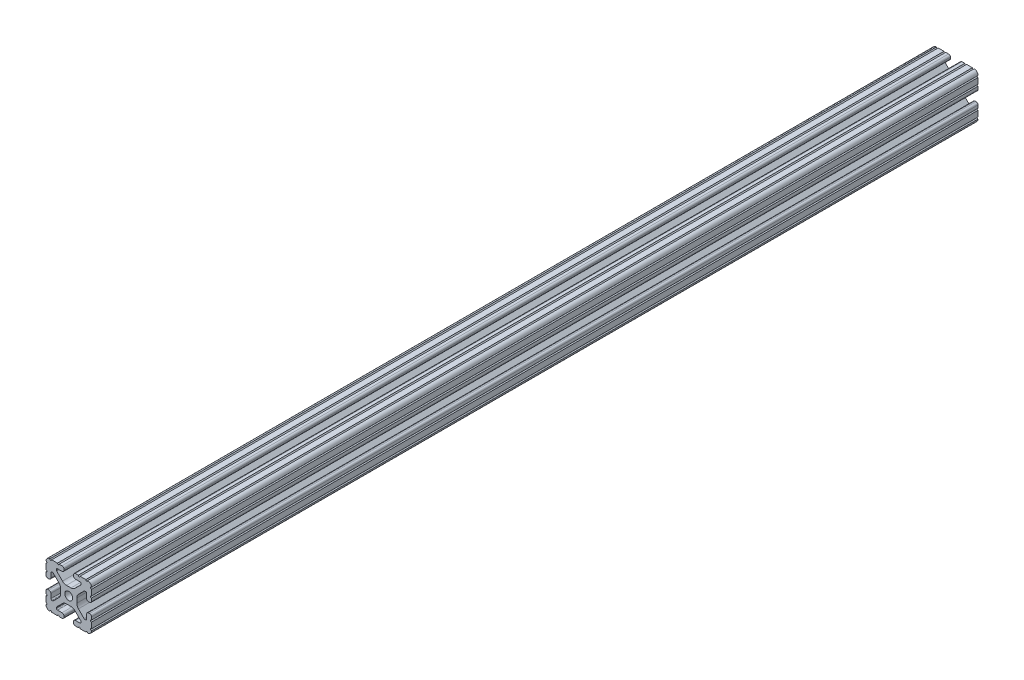
SolidWorks part; units mm, degrees
ref_plane "Front Plane" through (0, 0, 0) normal (0, 0, 1) x (1, 0, 0)
ref_plane "Top Plane" through (0, 0, 0) normal (0, 1, 0) x (1, 0, 0)
ref_plane "Right Plane" through (0, 0, 0) normal (1, 0, 0) x (0, 0, -1)
sketch "Sketch1" plane through (0, 0, 0) normal (0, 0, 1) x (1, 0, 0)
  line L0 (-4.064, 19.05) -> (-4.064, -19.05) construction
  line L1 (-19.05, -19.05) -> (19.05, -19.05) construction
  line L2 (-19.05, -19.05) -> (-19.05, 19.05) construction
  line L3 (-19.05, 19.05) -> (19.05, 19.05) construction
  line L4 (19.05, -19.05) -> (19.05, 19.05) construction
  line L5 (0, 19.05) -> (0, -19.05) construction
  line L6 (-19.05, 0) -> (19.05, 0) construction
  line L7 (-4.064, -19.05) -> (4.064, 19.05) construction
  line L8 (4.064, 19.05) -> (4.064, -19.05) construction
  circle A0 centre (0, 0) radius 3.3274
  point P0 (0, 0)
  line B0 (-10.287, 13.5524) -> (-10.287, 14.0843)
  line B1 (-9.3853, 14.986) -> (-5.6176, 14.986)
  line B2 (-4.064, 16.5396) -> (-4.064, 17.4964)
  line B3 (-5.6176, 19.05) -> (-7.9742, 19.05)
  line B4 (-9.4982, 19.05) -> (-14.3277, 19.05)
  line B5 (-19.05, 14.3277) -> (-19.05, 9.4961)
  line B6 (-19.05, 7.9763) -> (-19.05, 5.6176)
  line B7 (-17.4964, 4.064) -> (-16.5396, 4.064)
  line B8 (-14.986, 5.6176) -> (-14.986, 9.3853)
  line B9 (-14.0843, 10.287) -> (-13.516, 10.287)
  line B10 (-12.8784, 10.0229) -> (-8.1476, 5.2921)
  line B11 (-6.7564, 1.9335) -> (-6.7564, -1.9335)
  line B12 (-8.1476, -5.2921) -> (-12.8784, -10.0229)
  line B13 (-13.516, -10.287) -> (-14.0843, -10.287)
  line B14 (-14.986, -9.3853) -> (-14.986, -5.6176)
  line B15 (-16.5396, -4.064) -> (-17.4964, -4.064)
  line B16 (-19.05, -5.6176) -> (-19.05, -7.9763)
  line B17 (-19.05, -9.4961) -> (-19.05, -14.3277)
  line B18 (-14.3277, -19.05) -> (-9.4961, -19.05)
  line B19 (-7.9763, -19.05) -> (-5.6176, -19.05)
  line B20 (-4.064, -17.4964) -> (-4.064, -16.5396)
  line B21 (-5.6176, -14.986) -> (-9.3853, -14.986)
  line B22 (-10.287, -14.0843) -> (-10.287, -13.5524)
  line B23 (-10.0229, -12.9148) -> (-5.2522, -8.144)
  line B24 (-1.9022, -6.7564) -> (1.9022, -6.7564)
  line B25 (5.2522, -8.144) -> (10.0229, -12.9148)
  line B26 (10.287, -13.5524) -> (10.287, -14.0843)
  line B27 (9.3853, -14.986) -> (5.6176, -14.986)
  line B28 (4.064, -16.5396) -> (4.064, -17.4964)
  line B29 (5.6176, -19.05) -> (7.9763, -19.05)
  line B30 (9.4961, -19.05) -> (14.3277, -19.05)
  line B31 (19.05, -14.3277) -> (19.05, -9.4961)
  line B32 (19.05, -7.9763) -> (19.05, -5.6176)
  line B33 (17.4964, -4.064) -> (16.5396, -4.064)
  line B34 (14.986, -5.6176) -> (14.986, -9.3853)
  line B35 (14.0843, -10.287) -> (13.516, -10.287)
  line B36 (12.8784, -10.0229) -> (8.1476, -5.2921)
  line B37 (6.7564, -1.9335) -> (6.7564, 1.9335)
  line B38 (8.1476, 5.2921) -> (12.8784, 10.0229)
  line B39 (13.516, 10.287) -> (14.0843, 10.287)
  line B40 (14.986, 9.3853) -> (14.986, 5.6176)
  line B41 (16.5396, 4.064) -> (17.4964, 4.064)
  line B42 (19.05, 5.6176) -> (19.05, 7.9763)
  line B43 (19.05, 9.4961) -> (19.05, 14.3277)
  line B44 (14.3277, 19.05) -> (9.4982, 19.05)
  line B45 (7.9742, 19.05) -> (5.6176, 19.05)
  line B46 (4.064, 17.4964) -> (4.064, 16.5396)
  line B47 (5.6176, 14.986) -> (9.3853, 14.986)
  line B48 (10.287, 14.0843) -> (10.287, 13.5524)
  line B49 (10.0229, 12.9148) -> (5.2522, 8.144)
  line B50 (1.9022, 6.7564) -> (-1.9022, 6.7564)
  line B51 (-5.2522, 8.144) -> (-10.0229, 12.9148)
  circle B52 centre (0, 0) radius 3.3274
  arc B53 (-5.6176, 14.986) -> (-4.064, 16.5396) centre (-5.6176, 16.5396) ccw
  arc B54 (-4.064, 17.4964) -> (-5.6176, 19.05) centre (-5.6176, 17.4964) ccw
  arc B55 (-9.4982, 19.05) -> (-7.9742, 19.05) centre (-8.7362, 19.05) ccw
  arc B56 (-15.8475, 19.05) -> (-14.3277, 19.05) centre (-15.0876, 18.9933) ccw
  arc B57 (-15.8475, 19.05) -> (-19.05, 15.8475) centre (-15.8751, 15.8751) ccw
  arc B58 (-19.05, 14.3277) -> (-19.05, 15.8475) centre (-18.9933, 15.0876) ccw
  arc B59 (-19.05, 7.9763) -> (-19.05, 9.4961) centre (-18.9933, 8.7362) ccw
  arc B60 (-19.05, 5.6176) -> (-17.4964, 4.064) centre (-17.4964, 5.6176) ccw
  arc B61 (-16.5396, 4.064) -> (-14.986, 5.6176) centre (-16.5396, 5.6176) ccw
  arc B62 (-14.0843, 10.287) -> (-14.986, 9.3853) centre (-14.0843, 9.3853) ccw
  arc B63 (-12.8784, 10.0229) -> (-13.516, 10.287) centre (-13.516, 9.3853) ccw
  arc B64 (-6.7564, 1.9335) -> (-8.1476, 5.2921) centre (-11.5062, 1.9335) ccw
  arc B65 (-8.1476, -5.2921) -> (-6.7564, -1.9335) centre (-11.5062, -1.9335) ccw
  arc B66 (-13.516, -10.287) -> (-12.8784, -10.0229) centre (-13.516, -9.3853) ccw
  arc B67 (-14.986, -9.3853) -> (-14.0843, -10.287) centre (-14.0843, -9.3853) ccw
  arc B68 (-14.986, -5.6176) -> (-16.5396, -4.064) centre (-16.5396, -5.6176) ccw
  arc B69 (-17.4964, -4.064) -> (-19.05, -5.6176) centre (-17.4964, -5.6176) ccw
  arc B70 (-19.05, -9.4961) -> (-19.05, -7.9763) centre (-18.9933, -8.7362) ccw
  arc B71 (-19.05, -15.8475) -> (-19.05, -14.3277) centre (-18.9933, -15.0876) ccw
  arc B72 (-19.05, -15.8475) -> (-15.8475, -19.05) centre (-15.8751, -15.8751) ccw
  arc B73 (-14.3277, -19.05) -> (-15.8475, -19.05) centre (-15.0876, -18.9933) ccw
  arc B74 (-7.9763, -19.05) -> (-9.4961, -19.05) centre (-8.7362, -18.9933) ccw
  arc B75 (-5.6176, -19.05) -> (-4.064, -17.4964) centre (-5.6176, -17.4964) ccw
  arc B76 (-4.064, -16.5396) -> (-5.6176, -14.986) centre (-5.6176, -16.5396) ccw
  arc B77 (-10.287, -14.0843) -> (-9.3853, -14.986) centre (-9.3853, -14.0843) ccw
  arc B78 (-10.0229, -12.9148) -> (-10.287, -13.5524) centre (-9.3853, -13.5524) ccw
  arc B79 (-1.9022, -6.7564) -> (-5.2522, -8.144) centre (-1.9022, -11.494) ccw
  arc B80 (5.2522, -8.144) -> (1.9022, -6.7564) centre (1.9022, -11.494) ccw
  arc B81 (10.287, -13.5524) -> (10.0229, -12.9148) centre (9.3853, -13.5524) ccw
  arc B82 (9.3853, -14.986) -> (10.287, -14.0843) centre (9.3853, -14.0843) ccw
  arc B83 (5.6176, -14.986) -> (4.064, -16.5396) centre (5.6176, -16.5396) ccw
  arc B84 (4.064, -17.4964) -> (5.6176, -19.05) centre (5.6176, -17.4964) ccw
  arc B85 (9.4961, -19.05) -> (7.9763, -19.05) centre (8.7362, -18.9933) ccw
  arc B86 (15.8475, -19.05) -> (14.3277, -19.05) centre (15.0876, -18.9933) ccw
  arc B87 (15.8475, -19.05) -> (19.05, -15.8475) centre (15.8751, -15.8751) ccw
  arc B88 (19.05, -14.3277) -> (19.05, -15.8475) centre (18.9933, -15.0876) ccw
  arc B89 (19.05, -7.9763) -> (19.05, -9.4961) centre (18.9933, -8.7362) ccw
  arc B90 (19.05, -5.6176) -> (17.4964, -4.064) centre (17.4964, -5.6176) ccw
  arc B91 (16.5396, -4.064) -> (14.986, -5.6176) centre (16.5396, -5.6176) ccw
  arc B92 (14.0843, -10.287) -> (14.986, -9.3853) centre (14.0843, -9.3853) ccw
  arc B93 (12.8784, -10.0229) -> (13.516, -10.287) centre (13.516, -9.3853) ccw
  arc B94 (6.7564, -1.9335) -> (8.1476, -5.2921) centre (11.5062, -1.9335) ccw
  arc B95 (8.1476, 5.2921) -> (6.7564, 1.9335) centre (11.5062, 1.9335) ccw
  arc B96 (13.516, 10.287) -> (12.8784, 10.0229) centre (13.516, 9.3853) ccw
  arc B97 (14.986, 9.3853) -> (14.0843, 10.287) centre (14.0843, 9.3853) ccw
  arc B98 (14.986, 5.6176) -> (16.5396, 4.064) centre (16.5396, 5.6176) ccw
  arc B99 (17.4964, 4.064) -> (19.05, 5.6176) centre (17.4964, 5.6176) ccw
  arc B100 (19.05, 9.4961) -> (19.05, 7.9763) centre (18.9933, 8.7362) ccw
  arc B101 (19.05, 15.8475) -> (19.05, 14.3277) centre (18.9933, 15.0876) ccw
  arc B102 (19.05, 15.8475) -> (15.8475, 19.05) centre (15.8751, 15.8751) ccw
  arc B103 (14.3277, 19.05) -> (15.8475, 19.05) centre (15.0876, 18.9933) ccw
  arc B104 (7.9742, 19.05) -> (9.4982, 19.05) centre (8.7362, 19.05) ccw
  arc B105 (5.6176, 19.05) -> (4.064, 17.4964) centre (5.6176, 17.4964) ccw
  arc B106 (4.064, 16.5396) -> (5.6176, 14.986) centre (5.6176, 16.5396) ccw
  arc B107 (10.287, 14.0843) -> (9.3853, 14.986) centre (9.3853, 14.0843) ccw
  arc B108 (10.0229, 12.9148) -> (10.287, 13.5524) centre (9.3853, 13.5524) ccw
  arc B109 (1.9022, 6.7564) -> (5.2522, 8.144) centre (1.9022, 11.494) ccw
  arc B110 (-5.2522, 8.144) -> (-1.9022, 6.7564) centre (-1.9022, 11.494) ccw
  arc B111 (-10.287, 13.5524) -> (-10.0229, 12.9148) centre (-9.3853, 13.5524) ccw
  dimension "Center Hole Diameter" = 6.6548
  dimension "Rail Width" = 38.1
  dimension "Rail Height" = 38.1
  dimension "T-Slot Width" = 8.128
sketch_block_instance "Block1-1"
sketch_block "Block1"
sketch "Sketch2" plane through (0, 0, 0) normal (1, 0, 0) x (0, 0, -1)
  line L0 (-457.2, 0) -> (457.2, 0) construction
  line L1 (-406.4, 0) -> (-406.4, 19.05) construction
  line L2 (-406.4, 19.05) -> (406.4, 19.05) construction
  line L3 (406.4, 19.05) -> (406.4, 0) construction
  dimension "D1" = 50.8
  dimension "Length" = 914.4
sketch "Sketch3" plane through (0, 0, 0) normal (0, 0, 1) x (1, 0, 0)
  line L0 (-4.064, 16.5396) -> (-4.064, 17.4964) construction
  line L1 (-9.3853, 14.986) -> (-5.6176, 14.986) construction
  line L2 (-10.287, 13.5524) -> (-10.287, 14.0843) construction
  line L3 (-5.2522, 8.144) -> (-10.0229, 12.9148) construction
  line L4 (1.9022, 6.7564) -> (-1.9022, 6.7564) construction
  line L5 (10.0229, 12.9148) -> (5.2522, 8.144) construction
  line L6 (10.287, 14.0843) -> (10.287, 13.5524) construction
  line L7 (5.6176, 14.986) -> (9.3853, 14.986) construction
  line L8 (4.064, 17.4964) -> (4.064, 16.5396) construction
  line L9 (7.9742, 19.05) -> (5.6176, 19.05) construction
  line L10 (14.3277, 19.05) -> (9.4982, 19.05) construction
  line L11 (19.05, 9.4961) -> (19.05, 14.3277) construction
  line L12 (19.05, 5.6176) -> (19.05, 7.9763) construction
  line L13 (16.5396, 4.064) -> (17.4964, 4.064) construction
  line L14 (14.986, 9.3853) -> (14.986, 5.6176) construction
  line L15 (13.516, 10.287) -> (14.0843, 10.287) construction
  line L16 (8.1476, 5.2921) -> (12.8784, 10.0229) construction
  line L17 (6.7564, -1.9335) -> (6.7564, 1.9335) construction
  line L18 (12.8784, -10.0229) -> (8.1476, -5.2921) construction
  line L19 (14.0843, -10.287) -> (13.516, -10.287) construction
  line L20 (14.986, -5.6176) -> (14.986, -9.3853) construction
  line L21 (17.4964, -4.064) -> (16.5396, -4.064) construction
  line L22 (19.05, -7.9763) -> (19.05, -5.6176) construction
  line L23 (19.05, -14.3277) -> (19.05, -9.4961) construction
  line L24 (9.4961, -19.05) -> (14.3277, -19.05) construction
  line L25 (5.6176, -19.05) -> (7.9763, -19.05) construction
  line L26 (4.064, -16.5396) -> (4.064, -17.4964) construction
  line L27 (9.3853, -14.986) -> (5.6176, -14.986) construction
  line L28 (10.287, -13.5524) -> (10.287, -14.0843) construction
  line L29 (5.2522, -8.144) -> (10.0229, -12.9148) construction
  line L30 (-1.9022, -6.7564) -> (1.9022, -6.7564) construction
  line L31 (-10.0229, -12.9148) -> (-5.2522, -8.144) construction
  line L32 (-10.287, -14.0843) -> (-10.287, -13.5524) construction
  line L33 (-5.6176, -14.986) -> (-9.3853, -14.986) construction
  line L34 (-4.064, -17.4964) -> (-4.064, -16.5396) construction
  line L35 (-7.9763, -19.05) -> (-5.6176, -19.05) construction
  line L36 (-14.3277, -19.05) -> (-9.4961, -19.05) construction
  line L37 (-19.05, -9.4961) -> (-19.05, -14.3277) construction
  line L38 (-19.05, -5.6176) -> (-19.05, -7.9763) construction
  line L39 (-16.5396, -4.064) -> (-17.4964, -4.064) construction
  line L40 (-14.986, -9.3853) -> (-14.986, -5.6176) construction
  line L41 (-13.516, -10.287) -> (-14.0843, -10.287) construction
  line L42 (-8.1476, -5.2921) -> (-12.8784, -10.0229) construction
  line L43 (-6.7564, 1.9335) -> (-6.7564, -1.9335) construction
  line L44 (-12.8784, 10.0229) -> (-8.1476, 5.2921) construction
  line L45 (-14.0843, 10.287) -> (-13.516, 10.287) construction
  line L46 (-14.986, 5.6176) -> (-14.986, 9.3853) construction
  line L47 (-17.4964, 4.064) -> (-16.5396, 4.064) construction
  line L48 (-19.05, 7.9763) -> (-19.05, 5.6176) construction
  line L49 (-19.05, 14.3277) -> (-19.05, 9.4961) construction
  line L50 (-9.4982, 19.05) -> (-14.3277, 19.05) construction
  line L51 (-5.6176, 19.05) -> (-7.9742, 19.05) construction
  line L52 (-4.064, 16.5396) -> (-4.064, 17.4964)
  line L53 (-9.3853, 14.986) -> (-5.6176, 14.986)
  line L54 (-10.287, 13.5524) -> (-10.287, 14.0843)
  line L55 (-5.2522, 8.144) -> (-10.0229, 12.9148)
  line L56 (1.9022, 6.7564) -> (-1.9022, 6.7564)
  line L57 (10.0229, 12.9148) -> (5.2522, 8.144)
  line L58 (10.287, 14.0843) -> (10.287, 13.5524)
  line L59 (5.6176, 14.986) -> (9.3853, 14.986)
  line L60 (4.064, 17.4964) -> (4.064, 16.5396)
  line L61 (7.9742, 19.05) -> (5.6176, 19.05)
  line L62 (14.3277, 19.05) -> (9.4982, 19.05)
  line L63 (19.05, 9.4961) -> (19.05, 14.3277)
  line L64 (19.05, 5.6176) -> (19.05, 7.9763)
  line L65 (16.5396, 4.064) -> (17.4964, 4.064)
  line L66 (14.986, 9.3853) -> (14.986, 5.6176)
  line L67 (13.516, 10.287) -> (14.0843, 10.287)
  line L68 (8.1476, 5.2921) -> (12.8784, 10.0229)
  line L69 (6.7564, -1.9335) -> (6.7564, 1.9335)
  line L70 (12.8784, -10.0229) -> (8.1476, -5.2921)
  line L71 (14.0843, -10.287) -> (13.516, -10.287)
  line L72 (14.986, -5.6176) -> (14.986, -9.3853)
  line L73 (17.4964, -4.064) -> (16.5396, -4.064)
  line L74 (19.05, -7.9763) -> (19.05, -5.6176)
  line L75 (19.05, -14.3277) -> (19.05, -9.4961)
  line L76 (9.4961, -19.05) -> (14.3277, -19.05)
  line L77 (5.6176, -19.05) -> (7.9763, -19.05)
  line L78 (4.064, -16.5396) -> (4.064, -17.4964)
  line L79 (9.3853, -14.986) -> (5.6176, -14.986)
  line L80 (10.287, -13.5524) -> (10.287, -14.0843)
  line L81 (5.2522, -8.144) -> (10.0229, -12.9148)
  line L82 (-1.9022, -6.7564) -> (1.9022, -6.7564)
  line L83 (-10.0229, -12.9148) -> (-5.2522, -8.144)
  line L84 (-10.287, -14.0843) -> (-10.287, -13.5524)
  line L85 (-5.6176, -14.986) -> (-9.3853, -14.986)
  line L86 (-4.064, -17.4964) -> (-4.064, -16.5396)
  line L87 (-7.9763, -19.05) -> (-5.6176, -19.05)
  line L88 (-14.3277, -19.05) -> (-9.4961, -19.05)
  line L89 (-19.05, -9.4961) -> (-19.05, -14.3277)
  line L90 (-19.05, -5.6176) -> (-19.05, -7.9763)
  line L91 (-16.5396, -4.064) -> (-17.4964, -4.064)
  line L92 (-14.986, -9.3853) -> (-14.986, -5.6176)
  line L93 (-13.516, -10.287) -> (-14.0843, -10.287)
  line L94 (-8.1476, -5.2921) -> (-12.8784, -10.0229)
  line L95 (-6.7564, 1.9335) -> (-6.7564, -1.9335)
  line L96 (-12.8784, 10.0229) -> (-8.1476, 5.2921)
  line L97 (-14.0843, 10.287) -> (-13.516, 10.287)
  line L98 (-14.986, 5.6176) -> (-14.986, 9.3853)
  line L99 (-17.4964, 4.064) -> (-16.5396, 4.064)
  line L100 (-19.05, 7.9763) -> (-19.05, 5.6176)
  line L101 (-19.05, 14.3277) -> (-19.05, 9.4961)
  line L102 (-9.4982, 19.05) -> (-14.3277, 19.05)
  line L103 (-5.6176, 19.05) -> (-7.9742, 19.05)
  circle A0 centre (0, 0) radius 3.3274 construction
  circle A1 centre (0, 0) radius 3.3274
  circle A2 centre (0, 0) radius 3.3274
  arc A3 (-5.6176, 14.986) -> (-4.064, 16.5396) centre (-5.6176, 16.5396) ccw construction
  arc A4 (-9.3853, 14.986) -> (-10.287, 14.0843) centre (-9.3853, 14.0843) ccw construction
  arc A5 (-10.287, 13.5524) -> (-10.0229, 12.9148) centre (-9.3853, 13.5524) ccw construction
  arc A6 (-5.2522, 8.144) -> (-1.9022, 6.7564) centre (-1.9022, 11.494) ccw construction
  arc A7 (1.9022, 6.7564) -> (5.2522, 8.144) centre (1.9022, 11.494) ccw construction
  arc A8 (10.0229, 12.9148) -> (10.287, 13.5524) centre (9.3853, 13.5524) ccw construction
  arc A9 (10.287, 14.0843) -> (9.3853, 14.986) centre (9.3853, 14.0843) ccw construction
  arc A10 (4.064, 16.5396) -> (5.6176, 14.986) centre (5.6176, 16.5396) ccw construction
  arc A11 (5.6176, 19.05) -> (4.064, 17.4964) centre (5.6176, 17.4964) ccw construction
  arc A12 (7.9742, 19.05) -> (9.4982, 19.05) centre (8.7362, 19.05) ccw construction
  arc A13 (14.3277, 19.05) -> (15.8475, 19.05) centre (15.0876, 18.9933) ccw construction
  arc A14 (19.05, 15.8475) -> (15.8475, 19.05) centre (15.8751, 15.8751) ccw construction
  arc A15 (19.05, 15.8475) -> (19.05, 14.3277) centre (18.9933, 15.0876) ccw construction
  arc A16 (19.05, 9.4961) -> (19.05, 7.9763) centre (18.9933, 8.7362) ccw construction
  arc A17 (17.4964, 4.064) -> (19.05, 5.6176) centre (17.4964, 5.6176) ccw construction
  arc A18 (14.986, 5.6176) -> (16.5396, 4.064) centre (16.5396, 5.6176) ccw construction
  arc A19 (14.986, 9.3853) -> (14.0843, 10.287) centre (14.0843, 9.3853) ccw construction
  arc A20 (13.516, 10.287) -> (12.8784, 10.0229) centre (13.516, 9.3853) ccw construction
  arc A21 (8.1476, 5.2921) -> (6.7564, 1.9335) centre (11.5062, 1.9335) ccw construction
  arc A22 (6.7564, -1.9335) -> (8.1476, -5.2921) centre (11.5062, -1.9335) ccw construction
  arc A23 (12.8784, -10.0229) -> (13.516, -10.287) centre (13.516, -9.3853) ccw construction
  arc A24 (14.0843, -10.287) -> (14.986, -9.3853) centre (14.0843, -9.3853) ccw construction
  arc A25 (16.5396, -4.064) -> (14.986, -5.6176) centre (16.5396, -5.6176) ccw construction
  arc A26 (19.05, -5.6176) -> (17.4964, -4.064) centre (17.4964, -5.6176) ccw construction
  arc A27 (19.05, -7.9763) -> (19.05, -9.4961) centre (18.9933, -8.7362) ccw construction
  arc A28 (19.05, -14.3277) -> (19.05, -15.8475) centre (18.9933, -15.0876) ccw construction
  arc A29 (15.8475, -19.05) -> (19.05, -15.8475) centre (15.8751, -15.8751) ccw construction
  arc A30 (15.8475, -19.05) -> (14.3277, -19.05) centre (15.0876, -18.9933) ccw construction
  arc A31 (9.4961, -19.05) -> (7.9763, -19.05) centre (8.7362, -18.9933) ccw construction
  arc A32 (4.064, -17.4964) -> (5.6176, -19.05) centre (5.6176, -17.4964) ccw construction
  arc A33 (5.6176, -14.986) -> (4.064, -16.5396) centre (5.6176, -16.5396) ccw construction
  arc A34 (9.3853, -14.986) -> (10.287, -14.0843) centre (9.3853, -14.0843) ccw construction
  arc A35 (10.287, -13.5524) -> (10.0229, -12.9148) centre (9.3853, -13.5524) ccw construction
  arc A36 (5.2522, -8.144) -> (1.9022, -6.7564) centre (1.9022, -11.494) ccw construction
  arc A37 (-1.9022, -6.7564) -> (-5.2522, -8.144) centre (-1.9022, -11.494) ccw construction
  arc A38 (-10.0229, -12.9148) -> (-10.287, -13.5524) centre (-9.3853, -13.5524) ccw construction
  arc A39 (-10.287, -14.0843) -> (-9.3853, -14.986) centre (-9.3853, -14.0843) ccw construction
  arc A40 (-4.064, -16.5396) -> (-5.6176, -14.986) centre (-5.6176, -16.5396) ccw construction
  arc A41 (-5.6176, -19.05) -> (-4.064, -17.4964) centre (-5.6176, -17.4964) ccw construction
  arc A42 (-7.9763, -19.05) -> (-9.4961, -19.05) centre (-8.7362, -18.9933) ccw construction
  arc A43 (-14.3277, -19.05) -> (-15.8475, -19.05) centre (-15.0876, -18.9933) ccw construction
  arc A44 (-19.05, -15.8475) -> (-15.8475, -19.05) centre (-15.8751, -15.8751) ccw construction
  arc A45 (-19.05, -15.8475) -> (-19.05, -14.3277) centre (-18.9933, -15.0876) ccw construction
  arc A46 (-19.05, -9.4961) -> (-19.05, -7.9763) centre (-18.9933, -8.7362) ccw construction
  arc A47 (-17.4964, -4.064) -> (-19.05, -5.6176) centre (-17.4964, -5.6176) ccw construction
  arc A48 (-14.986, -5.6176) -> (-16.5396, -4.064) centre (-16.5396, -5.6176) ccw construction
  arc A49 (-14.986, -9.3853) -> (-14.0843, -10.287) centre (-14.0843, -9.3853) ccw construction
  arc A50 (-13.516, -10.287) -> (-12.8784, -10.0229) centre (-13.516, -9.3853) ccw construction
  arc A51 (-8.1476, -5.2921) -> (-6.7564, -1.9335) centre (-11.5062, -1.9335) ccw construction
  arc A52 (-6.7564, 1.9335) -> (-8.1476, 5.2921) centre (-11.5062, 1.9335) ccw construction
  arc A53 (-12.8784, 10.0229) -> (-13.516, 10.287) centre (-13.516, 9.3853) ccw construction
  arc A54 (-14.0843, 10.287) -> (-14.986, 9.3853) centre (-14.0843, 9.3853) ccw construction
  arc A55 (-16.5396, 4.064) -> (-14.986, 5.6176) centre (-16.5396, 5.6176) ccw construction
  arc A56 (-19.05, 5.6176) -> (-17.4964, 4.064) centre (-17.4964, 5.6176) ccw construction
  arc A57 (-19.05, 7.9763) -> (-19.05, 9.4961) centre (-18.9933, 8.7362) ccw construction
  arc A58 (-19.05, 14.3277) -> (-19.05, 15.8475) centre (-18.9933, 15.0876) ccw construction
  arc A59 (-15.8475, 19.05) -> (-19.05, 15.8475) centre (-15.8751, 15.8751) ccw construction
  arc A60 (-15.8475, 19.05) -> (-14.3277, 19.05) centre (-15.0876, 18.9933) ccw construction
  arc A61 (-9.4982, 19.05) -> (-7.9742, 19.05) centre (-8.7362, 19.05) ccw construction
  arc A62 (-4.064, 17.4964) -> (-5.6176, 19.05) centre (-5.6176, 17.4964) ccw construction
  circle A63 centre (0, 0) radius 3.3274
  arc A64 (-5.6176, 14.986) -> (-4.064, 16.5396) centre (-5.6176, 16.5396) ccw
  arc A65 (-9.3853, 14.986) -> (-10.287, 14.0843) centre (-9.3853, 14.0843) ccw
  arc A66 (-10.287, 13.5524) -> (-10.0229, 12.9148) centre (-9.3853, 13.5524) ccw
  arc A67 (-5.2522, 8.144) -> (-1.9022, 6.7564) centre (-1.9022, 11.494) ccw
  arc A68 (1.9022, 6.7564) -> (5.2522, 8.144) centre (1.9022, 11.494) ccw
  arc A69 (10.0229, 12.9148) -> (10.287, 13.5524) centre (9.3853, 13.5524) ccw
  arc A70 (10.287, 14.0843) -> (9.3853, 14.986) centre (9.3853, 14.0843) ccw
  arc A71 (4.064, 16.5396) -> (5.6176, 14.986) centre (5.6176, 16.5396) ccw
  arc A72 (5.6176, 19.05) -> (4.064, 17.4964) centre (5.6176, 17.4964) ccw
  arc A73 (7.9742, 19.05) -> (9.4982, 19.05) centre (8.7362, 19.05) ccw
  arc A74 (14.3277, 19.05) -> (15.8475, 19.05) centre (15.0876, 18.9933) ccw
  arc A75 (19.05, 15.8475) -> (15.8475, 19.05) centre (15.8751, 15.8751) ccw
  arc A76 (19.05, 15.8475) -> (19.05, 14.3277) centre (18.9933, 15.0876) ccw
  arc A77 (19.05, 9.4961) -> (19.05, 7.9763) centre (18.9933, 8.7362) ccw
  arc A78 (17.4964, 4.064) -> (19.05, 5.6176) centre (17.4964, 5.6176) ccw
  arc A79 (14.986, 5.6176) -> (16.5396, 4.064) centre (16.5396, 5.6176) ccw
  arc A80 (14.986, 9.3853) -> (14.0843, 10.287) centre (14.0843, 9.3853) ccw
  arc A81 (13.516, 10.287) -> (12.8784, 10.0229) centre (13.516, 9.3853) ccw
  arc A82 (8.1476, 5.2921) -> (6.7564, 1.9335) centre (11.5062, 1.9335) ccw
  arc A83 (6.7564, -1.9335) -> (8.1476, -5.2921) centre (11.5062, -1.9335) ccw
  arc A84 (12.8784, -10.0229) -> (13.516, -10.287) centre (13.516, -9.3853) ccw
  arc A85 (14.0843, -10.287) -> (14.986, -9.3853) centre (14.0843, -9.3853) ccw
  arc A86 (16.5396, -4.064) -> (14.986, -5.6176) centre (16.5396, -5.6176) ccw
  arc A87 (19.05, -5.6176) -> (17.4964, -4.064) centre (17.4964, -5.6176) ccw
  arc A88 (19.05, -7.9763) -> (19.05, -9.4961) centre (18.9933, -8.7362) ccw
  arc A89 (19.05, -14.3277) -> (19.05, -15.8475) centre (18.9933, -15.0876) ccw
  arc A90 (15.8475, -19.05) -> (19.05, -15.8475) centre (15.8751, -15.8751) ccw
  arc A91 (15.8475, -19.05) -> (14.3277, -19.05) centre (15.0876, -18.9933) ccw
  arc A92 (9.4961, -19.05) -> (7.9763, -19.05) centre (8.7362, -18.9933) ccw
  arc A93 (4.064, -17.4964) -> (5.6176, -19.05) centre (5.6176, -17.4964) ccw
  arc A94 (5.6176, -14.986) -> (4.064, -16.5396) centre (5.6176, -16.5396) ccw
  arc A95 (9.3853, -14.986) -> (10.287, -14.0843) centre (9.3853, -14.0843) ccw
  arc A96 (10.287, -13.5524) -> (10.0229, -12.9148) centre (9.3853, -13.5524) ccw
  arc A97 (5.2522, -8.144) -> (1.9022, -6.7564) centre (1.9022, -11.494) ccw
  arc A98 (-1.9022, -6.7564) -> (-5.2522, -8.144) centre (-1.9022, -11.494) ccw
  arc A99 (-10.0229, -12.9148) -> (-10.287, -13.5524) centre (-9.3853, -13.5524) ccw
  arc A100 (-10.287, -14.0843) -> (-9.3853, -14.986) centre (-9.3853, -14.0843) ccw
  arc A101 (-4.064, -16.5396) -> (-5.6176, -14.986) centre (-5.6176, -16.5396) ccw
  arc A102 (-5.6176, -19.05) -> (-4.064, -17.4964) centre (-5.6176, -17.4964) ccw
  arc A103 (-7.9763, -19.05) -> (-9.4961, -19.05) centre (-8.7362, -18.9933) ccw
  arc A104 (-14.3277, -19.05) -> (-15.8475, -19.05) centre (-15.0876, -18.9933) ccw
  arc A105 (-19.05, -15.8475) -> (-15.8475, -19.05) centre (-15.8751, -15.8751) ccw
  arc A106 (-19.05, -15.8475) -> (-19.05, -14.3277) centre (-18.9933, -15.0876) ccw
  arc A107 (-19.05, -9.4961) -> (-19.05, -7.9763) centre (-18.9933, -8.7362) ccw
  arc A108 (-17.4964, -4.064) -> (-19.05, -5.6176) centre (-17.4964, -5.6176) ccw
  arc A109 (-14.986, -5.6176) -> (-16.5396, -4.064) centre (-16.5396, -5.6176) ccw
  arc A110 (-14.986, -9.3853) -> (-14.0843, -10.287) centre (-14.0843, -9.3853) ccw
  arc A111 (-13.516, -10.287) -> (-12.8784, -10.0229) centre (-13.516, -9.3853) ccw
  arc A112 (-8.1476, -5.2921) -> (-6.7564, -1.9335) centre (-11.5062, -1.9335) ccw
  arc A113 (-6.7564, 1.9335) -> (-8.1476, 5.2921) centre (-11.5062, 1.9335) ccw
  arc A114 (-12.8784, 10.0229) -> (-13.516, 10.287) centre (-13.516, 9.3853) ccw
  arc A115 (-14.0843, 10.287) -> (-14.986, 9.3853) centre (-14.0843, 9.3853) ccw
  arc A116 (-16.5396, 4.064) -> (-14.986, 5.6176) centre (-16.5396, 5.6176) ccw
  arc A117 (-19.05, 5.6176) -> (-17.4964, 4.064) centre (-17.4964, 5.6176) ccw
  arc A118 (-19.05, 7.9763) -> (-19.05, 9.4961) centre (-18.9933, 8.7362) ccw
  arc A119 (-19.05, 14.3277) -> (-19.05, 15.8475) centre (-18.9933, 15.0876) ccw
  arc A120 (-15.8475, 19.05) -> (-19.05, 15.8475) centre (-15.8751, 15.8751) ccw
  arc A121 (-15.8475, 19.05) -> (-14.3277, 19.05) centre (-15.0876, 18.9933) ccw
  arc A122 (-9.4982, 19.05) -> (-7.9742, 19.05) centre (-8.7362, 19.05) ccw
  arc A123 (-4.064, 17.4964) -> (-5.6176, 19.05) centre (-5.6176, 17.4964) ccw
  dimension "D1" = 0
extrude "Boss-Extrude1" add sketch "Sketch3" along normal up to vertex (457.2 mm away) and the other way up to vertex (457.2 mm away) contours L52 A123 L103 A122 L102 A121 A120 A119 L101 A118 L100 A117 L99 A116 L98 A115 L97 A114 L96 A113 L95 A112 L94 A111 L93 A110 L92 A109 L91 A108 L90 A107 L89 A106 A105 A104 L88 A103 L87 A102 L86 A101 L85 A100 L84 A99 L83 A98 L82 A97 L81 up to point (0, 0, 457.2) other way up to point (0, 0, -457.2)
sketch "Sketch4" plane through (0, 0, 0) normal (0, 1, 0) x (1, 0, 0)
  line L0 (-11.9129, 457.2) -> (-11.9129, -285.75) construction
  line L1 (-9.4982, 457.2) -> (-14.3277, 457.2) construction
  line L9 (-11.9129, -285.75) -> (-26.026, -285.75)
  line L10 (-26.026, -285.75) -> (-26.026, -467.5271)
  line L11 (-26.026, -467.5271) -> (32.6353, -467.5271)
  line L12 (32.6353, -467.5271) -> (32.6353, -285.75)
  line L13 (32.6353, -285.75) -> (-11.9129, -285.75)
extrude "Cut-Extrude1" cut sketch "Sketch4" against normal mid plane 45.72
